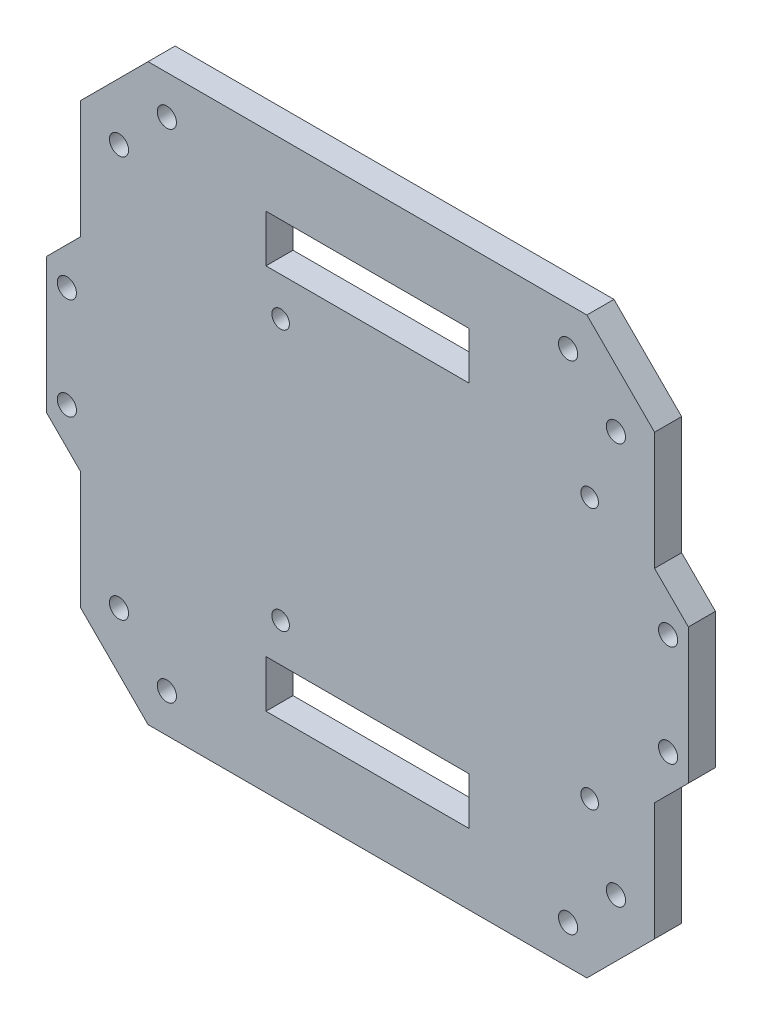
SolidWorks part; units mm, degrees
material "PETG CF"
ref_plane "Front Plane" through (0, 0, 0) normal (1, 0, 0) x (0, 1, 0)
ref_plane "Top Plane" through (0, 0, 0) normal (0, 0, 1) x (0, 1, 0)
ref_plane "Right Plane" through (0, 0, 0) normal (0, 1, 0) x (-1, 0, 0)
sketch "Sketch1" plane through (0, 0, 0) normal (0, 0, 1) x (0, 1, 0)
  line L5 (-41.1815, 53.8815) -> (-19.05, 53.8815)
  line L8 (53.8815, -53.8815) -> (19.05, -53.8815) construction
  line L17 (53.8815, -53.8815) -> (53.8815, 53.8815) construction
  line L18 (53.8815, 53.8815) -> (19.05, 53.8815) construction
  line L19 (-53.8815, -53.8815) -> (-53.8815, 53.8815) construction
  line L26 (-53.8815, 53.8815) -> (53.8815, -53.8815) construction
  line L27 (53.8815, 53.8815) -> (-53.8815, -53.8815) construction
  line L28 (41.1815, 53.8815) -> (53.8815, 41.1815)
  line L29 (53.8815, 41.1815) -> (53.8815, -41.1815)
  line L30 (53.8815, -41.1815) -> (41.1815, -53.8815)
  line L31 (41.1815, -53.8815) -> (19.05, -53.8815)
  line L32 (-41.1815, -53.8815) -> (-53.8815, -41.1815)
  line L33 (-53.8815, -41.1815) -> (-53.8815, 41.1815)
  line L34 (-53.8815, 41.1815) -> (-41.1815, 53.8815)
  line L35 (-46.6335, -37.6533) -> (-37.6533, -46.6335) construction
  line L40 (-19.05, -53.8815) -> (-12.7, -60.2315)
  line L42 (0, 67.1479) -> (0, -65.0754) construction
  line L43 (-75.0551, 0) -> (65.1963, 0) construction
  line L49 (-12.7, -60.2315) -> (12.7, -60.2315)
  line L50 (-24.5, 16.3) -> (24.5, 16.3) construction
  line L51 (-24.5, 16.3) -> (-24.5, -41.7) construction
  line L52 (-24.5, -41.7) -> (24.5, -41.7) construction
  line L53 (24.5, 16.3) -> (24.5, -41.7) construction
  line L54 (-24.5, 16.3) -> (24.5, -41.7) construction
  line L55 (-24.5, -41.7) -> (24.5, 16.3) construction
  line L58 (46.6335, 0) -> (-46.6335, 0) construction
  line L59 (12.7, -60.2315) -> (19.05, -53.8815)
  line L60 (-19.05, -53.8815) -> (-53.8815, -53.8815) construction
  line L61 (-19.05, -53.8815) -> (-41.1815, -53.8815)
  line L62 (-19.05, 53.8815) -> (-12.7, 60.2315)
  line L63 (-12.7, 60.2315) -> (12.7, 60.2315)
  line L64 (12.7, 60.2315) -> (19.05, 53.8815)
  line L65 (19.05, 53.8815) -> (41.1815, 53.8815)
  line L66 (-19.05, 53.8815) -> (-53.8815, 53.8815) construction
  line L67 (-9.525, -56.4215) -> (9.525, -56.4215) construction
  line L68 (-9.525, 56.4215) -> (9.525, 56.4215) construction
  line L69 (40.64, -19.05) -> (31.75, -19.05)
  line L70 (-40.64, 19.05) -> (-31.75, 19.05)
  line L71 (-40.64, 19.05) -> (-40.64, -19.05)
  line L72 (-40.64, -19.05) -> (-31.75, -19.05)
  line L73 (-31.75, 19.05) -> (-31.75, -19.05)
  line L74 (40.64, 19.05) -> (40.64, -19.05)
  line L75 (40.64, 19.05) -> (31.75, 19.05)
  line L76 (31.75, 19.05) -> (31.75, -19.05)
  circle A0 centre (-46.6335, -37.6533) radius 1.8
  circle A1 centre (-37.6533, -46.6335) radius 1.8
  circle A6 centre (46.6335, -37.6533) radius 1.8
  circle A7 centre (37.6533, -46.6335) radius 1.8
  circle A8 centre (-46.6335, 37.6533) radius 1.8
  circle A9 centre (-37.6533, 46.6335) radius 1.8
  circle A10 centre (37.6533, 46.6335) radius 1.8
  circle A11 centre (46.6335, 37.6533) radius 1.8
  circle A16 centre (-24.5, -41.7) radius 1.65
  circle A17 centre (24.5, -41.7) radius 1.65
  circle A18 centre (24.5, 16.3) radius 1.65
  circle A19 centre (-24.5, 16.3) radius 1.65
  circle A24 centre (-9.525, -56.4215) radius 1.8
  circle A25 centre (9.525, -56.4215) radius 1.8
  circle A26 centre (9.525, 56.4215) radius 1.8
  circle A27 centre (-9.525, 56.4215) radius 1.8
  point P0 (0, 0)
  point P5 (0, 0)
  point P8 (0, 0)
  point P20 (0, 0)
  point P23 (0, 0)
  point P24 (0, 0)
  point P40 (-42.1434, -42.1434)
  point P47 (0, -60.2315)
  point P59 (0, -56.4215)
  point P64 (0, 0)
  point P66 (0, -12.7)
  point P74 (-40.64, 0)
  dimension "D4" = 3.6
  dimension "D13" = 3.3
  dimension "D18" = 3.6
  dimension "D1" = 152.4
  dimension "D2" = 107.7631
  dimension "D5" = 12.7
  dimension "D6" = 12.7
  dimension "D8" = 45
  dimension "D9" = 58
  dimension "D10" = 49
  dimension "D11" = 7.62
  dimension "D12" = 12.7
  dimension "D7" = 6.35
  dimension "D14" = 38.1
  dimension "D15" = 6.35
  dimension "D16" = 6.35
  dimension "D17" = 19.05
  dimension "D19" = 3.81
  dimension "D3" = 38.1
  dimension "D20" = 8.89
  dimension "D21" = 31.75
extrude "Boss-Extrude1" add sketch "Sketch1" along normal mid plane 5.08
equation "\"Width\"= sqr ( ( \"Diagonal\" ^ 2 ) / 2 )"
equation "\"depth\"= 0.2in"
equation "\"D1@Boss-Extrude1\"=\"depth\""
equation "\"R1\"= 3mm'Radius of the standoffs for the wings (M5 screws)"
equation "\"Corner Spacing\"= 25in"
equation "\"Diagonal\"= 6'Diagonal measurements of the standoff"
equation "\"D1@Sketch1\"=\"Diagonal\""
equation "\"D4@Sketch1\" = \"R1\" + \"Tolerance\""
equation "\"R2.\"= 3mm'Radius of the standoffs for the RPI (M2 Screws)"
equation "\"Wing Standoff Spacing\"= 0.5"
equation "\"D6@Sketch1\"=\"Wing Standoff Spacing\""
equation "\"Distance away for the wing holes\"= .4in"
equation "\"D2@Sketch1\"=\"Width\""
equation "\"Tolerance\"= 0.6mm"
equation "\"R3\"= 2.7mm"
equation "\"D13@Sketch1\" = \"R3\" + \"Tolerance\""
equation "\"D18@Sketch1\"= \"R1\" + \"Tolerance\""
equation "\"Le\"=6"
